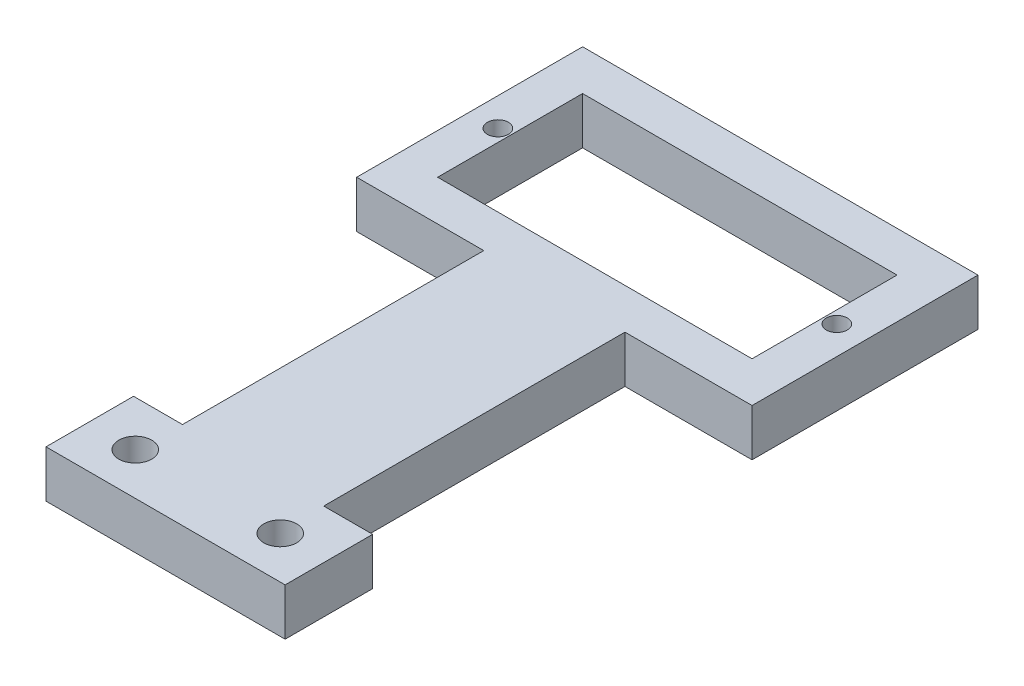
SolidWorks part; units mm, degrees
ref_plane "Front Plane" through (0, 0, 0) normal (0, 0, 1) x (1, 0, 0)
ref_plane "Top Plane" through (0, 0, 0) normal (0, 1, 0) x (1, 0, 0)
ref_plane "Right Plane" through (0, 0, 0) normal (1, 0, 0) x (0, 0, -1)
sketch "Sketch1" plane through (0, 0, 0) normal (0, 1, 0) x (1, 0, 0)
  line L1 (0, 0) -> (42, 0)
  line L2 (0, 0) -> (0, 24)
  line L3 (0, 24) -> (42, 24)
  line L4 (42, 0) -> (42, 24)
  dimension "D1" = 42
  dimension "D2" = 24
extrude "Boss-Extrude1" add sketch "Sketch1" along normal blind 5
sketch "Sketch2" plane through (0, 5, 0) normal (0, 1, 0) x (1, 0, 0)
  line L8 (4.3, 19.7) -> (4.3, 4.3)
  line L9 (4.3, 4.3) -> (37.7, 4.3)
  line L10 (37.7, 4.3) -> (37.7, 19.7)
  line L11 (37.7, 19.7) -> (4.3, 19.7)
  line L12 (4.3, 19.7) -> (4.3, 4.3)
  line L13 (4.3, 4.3) -> (37.7, 4.3)
  line L14 (37.7, 4.3) -> (37.7, 19.7)
  line L15 (37.7, 19.7) -> (4.3, 19.7)
  dimension "D1" = 4.3
extrude "Cut-Extrude1" cut sketch "Sketch2" against normal through all
sketch "Sketch3" plane through (0, 5, 0) normal (0, 1, 0) x (1, 0, 0)
  line L0 (0, 0) -> (42, 0) construction
  line L1 (28.5, 0) -> (13.5, 0)
  line L2 (28.5, 0) -> (28.5, -32)
  line L3 (28.5, -32) -> (13.5, -32)
  line L4 (13.5, 0) -> (13.5, -32)
  point P6 (21, 0)
  point P7 (21, 0)
  dimension "D1" = 15
  dimension "D2" = 32
extrude "Boss-Extrude2" add sketch "Sketch3" against normal up to surface (5 mm away) up to face at (21, 0, -12)
sketch "Sketch4" plane through (0, 5, 0) normal (0, 1, 0) x (1, 0, 0)
  line L0 (13.5, -32) -> (28.5, -32) construction
  line L1 (8.3, -32) -> (33.7, -32)
  line L2 (8.3, -32) -> (8.3, -41.3)
  line L3 (8.3, -41.3) -> (33.7, -41.3)
  line L4 (33.7, -32) -> (33.7, -41.3)
  point P6 (21, -32)
  point P7 (21, -32)
  dimension "D1" = 9.3
  dimension "D2" = 25.4
extrude "Boss-Extrude3" add sketch "Sketch4" against normal up to surface (5 mm away) up to face at (21, 0, -12)
sketch "Sketch5" plane through (0, 5, 0) normal (0, 1, 0) x (1, 0, 0)
  line L0 (8.3, -36.8178) -> (33.7, -36.8178) construction
  line L1 (8.3, -32) -> (8.3, -41.3) construction
  line L2 (33.7, -41.3) -> (33.7, -32) construction
  line L3 (8.3, -41.3) -> (33.7, -41.3) construction
  circle A0 centre (13.3, -36.8178) radius 1.75
  circle A1 centre (28.7, -36.8178) radius 1.75
  dimension "D4" = 3.5
  dimension "D5" = 3.5
  dimension "D1" = 4.4822
  dimension "D2" = 5
  dimension "D3" = 5
extrude "Cut-Extrude2" cut sketch "Sketch5" against normal through all
sketch "Sketch6" plane through (0, 5, 0) normal (0, 1, 0) x (1, 0, 0)
  line L0 (0, 12) -> (42, 12) construction
  line L1 (0, 24) -> (0, 0) construction
  line L2 (42, 0) -> (42, 24) construction
  circle A0 centre (3, 12) radius 1.115
  circle A1 centre (39, 12) radius 1.115
  point P6 (0, 12)
  point P11 (2.8007, 12)
  point P12 (2.859, 12)
  point P13 (3.034, 12)
  point P14 (2.859, 12)
  point P15 (0, 0)
  point P16 (21, 12)
  dimension "D2" = 2.23
  dimension "D1" = 36
  dimension "D3" = 18
extrude "Cut-Extrude3" cut sketch "Sketch6" against normal through all
